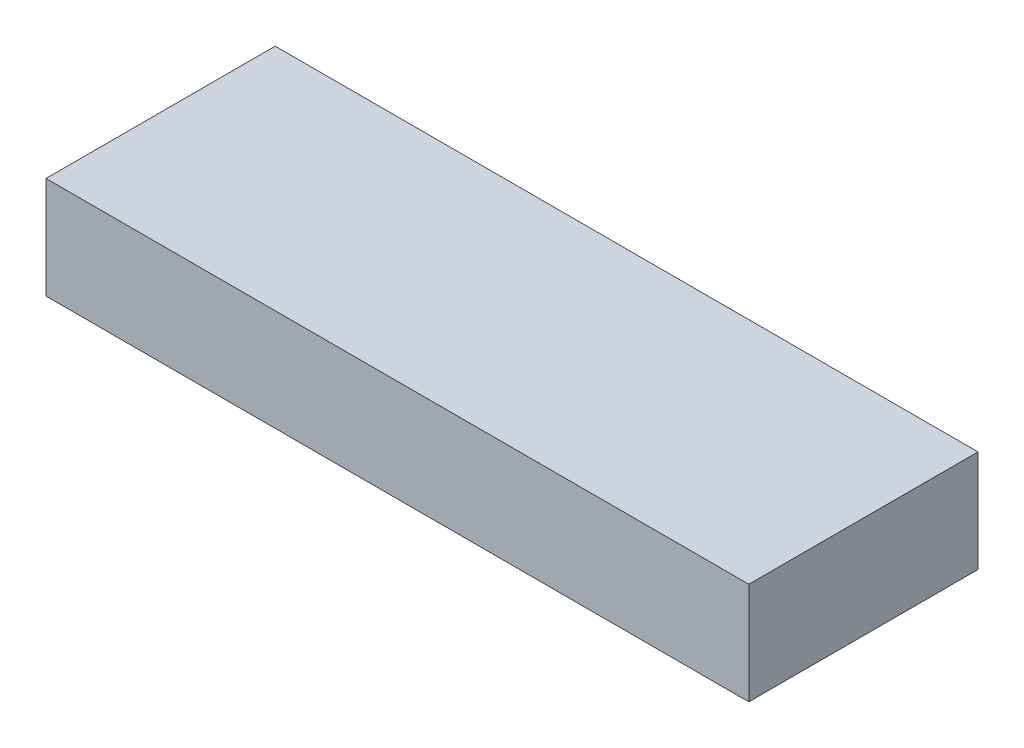
SolidWorks part; units mm, degrees
ref_plane "Front Plane" through (0, 0, 0) normal (0, 0, 1) x (1, 0, 0)
ref_plane "Top Plane" through (0, 0, 0) normal (0, 1, 0) x (1, 0, 0)
ref_plane "Right Plane" through (0, 0, 0) normal (1, 0, 0) x (0, 0, -1)
sketch "Sketch1" plane through (0, 0, 0) normal (0, 1, 0) x (1, 0, 0)
  line L0 (0, 0) -> (138, 0)
  line L1 (138, 0) -> (138, 45)
  line L2 (138, 45) -> (0, 45)
  line L3 (0, 45) -> (0, 0)
extrude "Boss-Extrude1" add sketch "Sketch1" along normal blind 20
